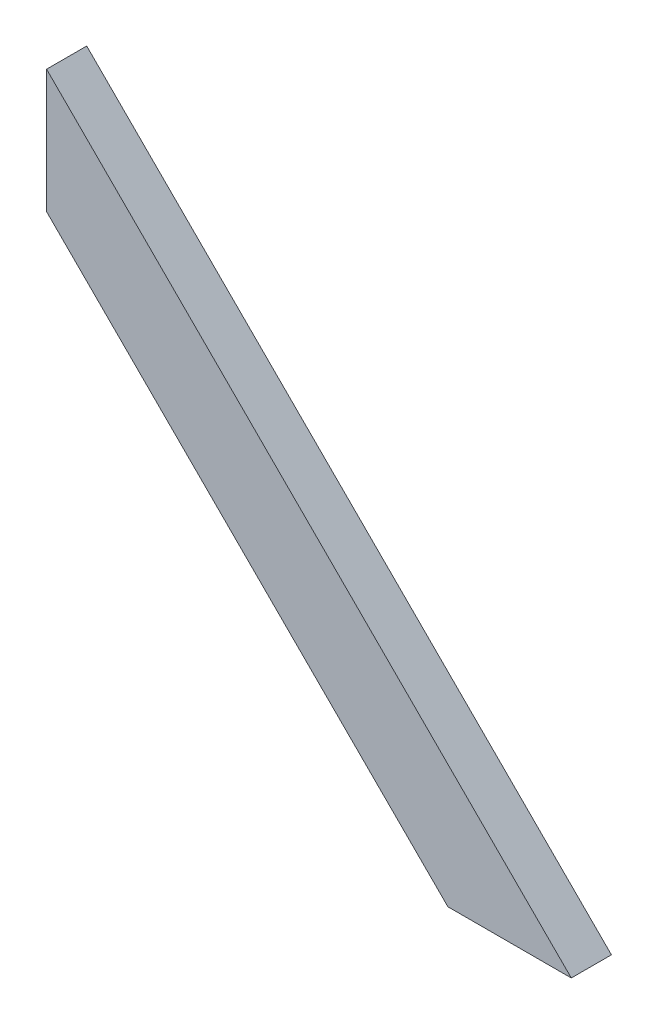
SolidWorks part; units mm, degrees
ref_plane "Front Plane" through (0, 0, 0) normal (0, 0, 1) x (1, 0, 0)
ref_plane "Top Plane" through (0, 0, 0) normal (0, 1, 0) x (1, 0, 0)
ref_plane "Right Plane" through (0, 0, 0) normal (1, 0, 0) x (0, 0, -1)
sketch "Sketch1" plane through (0, 0, 0) normal (0, 0, 1) x (1, 0, 0)
  line L0 (0, 277.4401) -> (0, -148.4939) construction
  line L1 (-89.6341, -98.4939) -> (364.3971, -98.4939) construction
  line L2 (0, 131.5061) -> (230, -98.4939)
  line L3 (152.4455, -176.0484) -> (368.2426, 39.7487) construction
  line L4 (-70.4758, 61.0303) -> (63.592, 195.098) construction
  line L5 (230, -98.4939) -> (300.7107, -98.4939)
  line L6 (300.7107, -98.4939) -> (0, 202.2168)
  line L7 (0, 202.2168) -> (0, 131.5061)
  point P5 (0, 131.5061)
  point P6 (230, -98.4939)
  dimension "D1" = 50
  dimension "D2" = 230
  dimension "D3" = 230
  dimension "D4" = 45
  dimension "D5" = 45
  dimension "D6" = 50
  dimension "D7" = 325.2691
  dimension "D8" = 300.7107
  dimension "D9" = 300.7107
  dimension "D10" = 425.2691
extrude "Boss-Extrude1" add sketch "Sketch1" along normal blind 23
